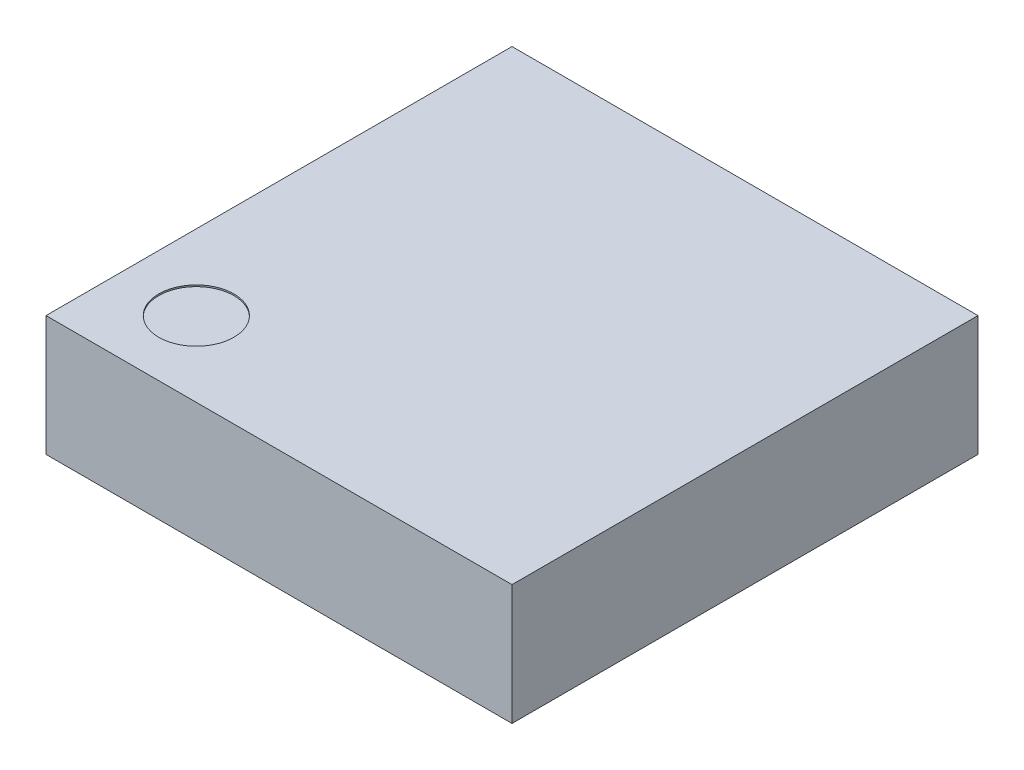
SolidWorks part; units mm, degrees
ref_plane "Front Plane" through (0, 0, 0) normal (0, 0, 1) x (1, 0, 0)
ref_plane "Top Plane" through (0, 0, 0) normal (0, 1, 0) x (1, 0, 0)
ref_plane "Right Plane" through (0, 0, 0) normal (1, 0, 0) x (0, 0, -1)
sketch "Sketch1" plane through (0, 0, 0) normal (0, 1, 0) x (1, 0, 0)
  line L1 (-1.55, -1.55) -> (1.55, -1.55)
  line L2 (-1.55, -1.55) -> (-1.55, 1.55)
  line L3 (-1.55, 1.55) -> (1.55, 1.55)
  line L4 (1.55, -1.55) -> (1.55, 1.55)
  line L5 (-1.55, -1.55) -> (1.55, 1.55) construction
  line L6 (-1.55, 1.55) -> (1.55, -1.55) construction
  point P0 (0, 0)
  dimension "D1" = 3.1
extrude "Boss-Extrude1" add sketch "Sketch1" along normal blind 0.8
sketch "Sketch2" plane through (0, 0.8, 0) normal (0, 1, 0) x (1, 0, 0)
  line L0 (-1.55, -1.55) -> (1.55, -1.55) construction
  line L1 (-1.55, 1.55) -> (-1.55, -1.55) construction
  circle A0 centre (-1.05, -1.05) radius 0.25
  dimension "D3" = 0.5
  dimension "D1" = 0.5
  dimension "D2" = 0.5
extrude "Cut-Extrude1" cut sketch "Sketch2" against normal blind 0.01
